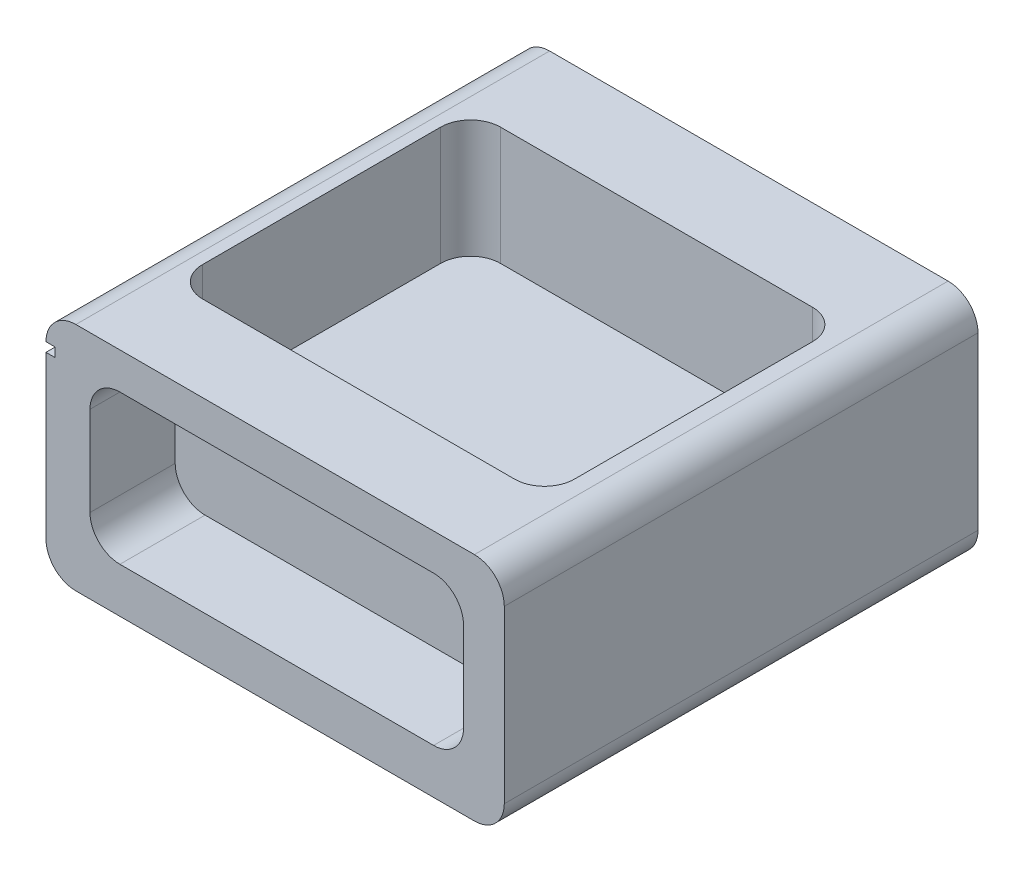
SolidWorks part; units mm, degrees
ref_plane "Front Plane" through (0, 0, 0) normal (0, 0, 1) x (1, 0, 0)
ref_plane "Top Plane" through (0, 0, 0) normal (0, 1, 0) x (1, 0, 0)
ref_plane "Right Plane" through (0, 0, 0) normal (1, 0, 0) x (0, 0, -1)
sketch "Sketch1" plane through (0, 0, 0) normal (0, 0, 1) x (1, 0, 0)
  line L1 (-72.8197, 29.5545) -> (-5.08, 29.5545)
  line L2 (-77.8997, 24.4745) -> (-77.8997, -4.5891)
  line L3 (-72.8197, -9.6691) -> (-5.08, -9.6691)
  line L4 (0, 24.4745) -> (0, -4.5891)
  line L7 (-65.3399, 23.3517) -> (-12.0125, 23.3517)
  line L8 (-70.4199, 18.2717) -> (-70.4199, 3.0732)
  line L9 (-65.3399, -2.0068) -> (-12.0125, -2.0068)
  line L10 (-6.9325, 18.2717) -> (-6.9325, 3.0732)
  arc A0 (-77.8997, -4.5891) -> (-72.8197, -9.6691) centre (-72.8197, -4.5891) ccw
  arc A1 (-5.08, -9.6691) -> (0, -4.5891) centre (-5.08, -4.5891) ccw
  arc A2 (-5.08, 29.5545) -> (0, 24.4745) centre (-5.08, 24.4745) cw
  arc A3 (-72.8197, 29.5545) -> (-77.8997, 24.4745) centre (-72.8197, 24.4745) ccw
  arc A4 (-70.4199, 3.0732) -> (-65.3399, -2.0068) centre (-65.3399, 3.0732) ccw
  arc A5 (-12.0125, -2.0068) -> (-6.9325, 3.0732) centre (-12.0125, 3.0732) ccw
  arc A6 (-12.0125, 23.3517) -> (-6.9325, 18.2717) centre (-12.0125, 18.2717) cw
  arc A7 (-70.4199, 18.2717) -> (-65.3399, 23.3517) centre (-65.3399, 18.2717) cw
  dimension "D1" = 5.08
  dimension "D2" = 5.08
extrude "Boss-Extrude1" add sketch "Sketch1" along normal blind 14.478
sketch "Sketch2" plane through (0, 0, 0) normal (0, 0, -1) x (-1, 0, 0)
  line L1 (5.08, 29.5545) -> (72.8197, 29.5545)
  line L2 (0, 24.4745) -> (0, -4.5891)
  line L3 (5.08, -9.6691) -> (72.8197, -9.6691)
  line L4 (77.8997, 24.4745) -> (77.8997, -4.5891)
  arc A0 (0, -4.5891) -> (5.08, -9.6691) centre (5.08, -4.5891) ccw
  arc A1 (72.8197, -9.6691) -> (77.8997, -4.5891) centre (72.8197, -4.5891) ccw
  arc A2 (72.8197, 29.5545) -> (77.8997, 24.4745) centre (72.8197, 24.4745) cw
  arc A3 (5.08, 29.5545) -> (0, 24.4745) centre (5.08, 24.4745) ccw
  dimension "D1" = 5.08
extrude "Boss-Extrude2" add sketch "Sketch2" along normal blind 66.04
sketch "Sketch3" plane through (-77.8997, 0, 0) normal (-1, 0, 0) x (0, 0, 1)
  line L0 (14.478, 24.4745) -> (14.478, -4.5891) construction
  line L1 (-66.04, 24.4745) -> (14.478, 24.4745)
  line L2 (-66.04, 24.4745) -> (-66.04, 22.9974)
  line L3 (-66.04, 22.9974) -> (14.478, 22.9974)
  line L4 (14.478, 24.4745) -> (14.478, 22.9974)
extrude "Boss-Extrude3" add sketch "Sketch3" against normal blind 1.524
sketch "Sketch4" plane through (-77.8997, 0, 0) normal (-1, 0, 0) x (0, 0, 1)
  line L0 (14.478, 24.4745) -> (14.478, -4.5891) construction
  line L1 (-66.04, 24.4745) -> (14.478, 24.4745)
  line L2 (-66.04, 24.4745) -> (-66.04, 22.9148)
  line L3 (-66.04, 22.9148) -> (14.478, 22.9148)
  line L4 (14.478, 24.4745) -> (14.478, 22.9148)
extrude "Cut-Extrude1" cut sketch "Sketch4" against normal blind 1.524
sketch "Sketch8" plane through (0, 0.3998, -66.04) normal (0, 0, -1) x (-1, 0, 0)
  line L1 (13.8133, 22.1732) -> (64.646, 22.1732)
  line L2 (8.7333, 17.0932) -> (8.7333, 3.7514)
  line L3 (13.8133, -1.3286) -> (64.646, -1.3286)
  line L4 (69.726, 17.0932) -> (69.726, 3.7514)
  arc A0 (8.7333, 3.7514) -> (13.8133, -1.3286) centre (13.8133, 3.7514) ccw
  arc A1 (69.726, 3.7514) -> (64.646, -1.3286) centre (64.646, 3.7514) cw
  arc A2 (64.646, 22.1732) -> (69.726, 17.0932) centre (64.646, 17.0932) cw
  arc A3 (13.8133, 22.1732) -> (8.7333, 17.0932) centre (13.8133, 17.0932) ccw
  dimension "D1" = 5.08
extrude "Cut-Extrude3" cut sketch "Sketch8" against normal blind 14.478
sketch "Sketch10" plane through (0, 29.5545, 6.7927) normal (0, 1, 0) x (1, 0, 0)
  line L1 (-65.7955, 57.4579) -> (-12.762, 57.4579)
  line L2 (-70.8755, 52.3779) -> (-70.8755, 11.9138)
  line L3 (-65.7955, 6.8338) -> (-12.762, 6.8338)
  line L4 (-7.682, 52.3779) -> (-7.682, 11.9138)
  arc A0 (-70.8755, 11.9138) -> (-65.7955, 6.8338) centre (-65.7955, 11.9138) ccw
  arc A1 (-12.762, 6.8338) -> (-7.682, 11.9138) centre (-12.762, 11.9138) ccw
  arc A2 (-12.762, 57.4579) -> (-7.682, 52.3779) centre (-12.762, 52.3779) cw
  arc A3 (-65.7955, 57.4579) -> (-70.8755, 52.3779) centre (-65.7955, 52.3779) ccw
  dimension "D1" = 5.08
extrude "Cut-Extrude6" cut sketch "Sketch10" against normal blind 20.066
